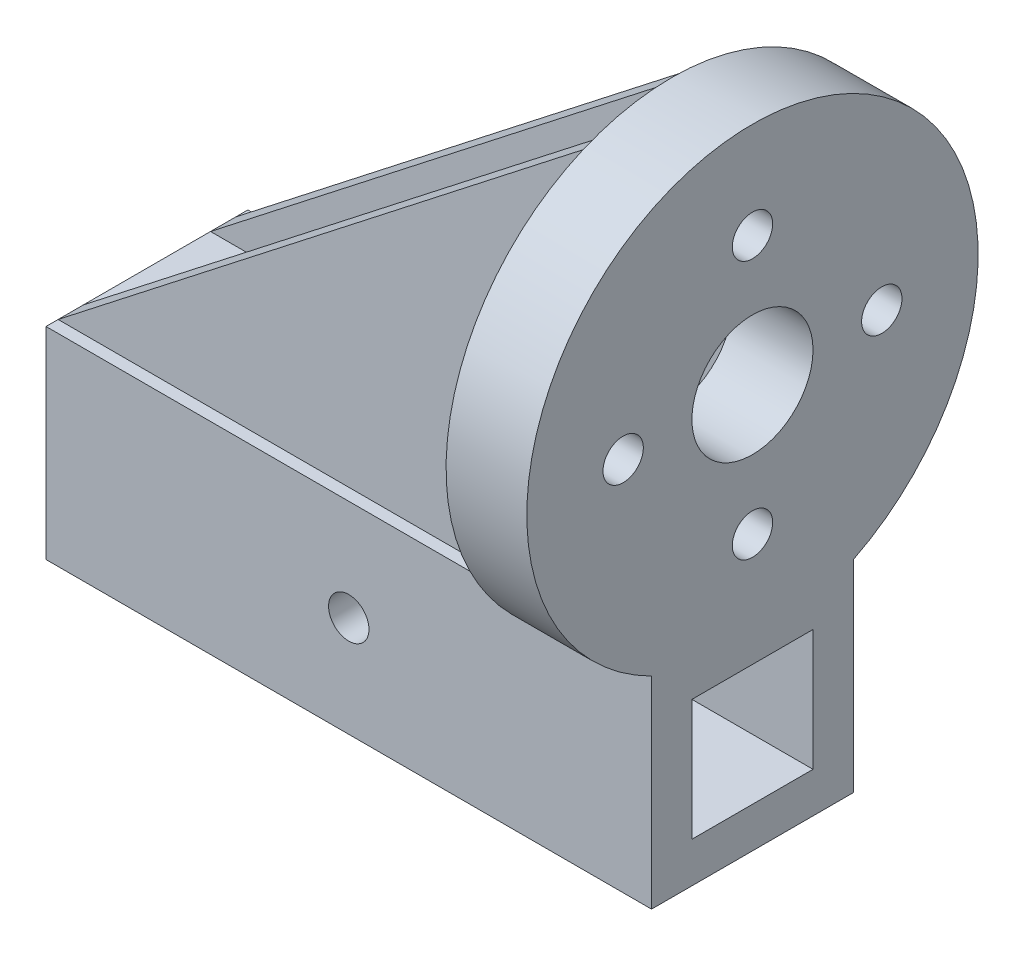
SolidWorks part; units mm, degrees
ref_plane "Front Plane" through (0, 0, 0) normal (0, 0, 1) x (1, 0, 0)
ref_plane "Top Plane" through (0, 0, 0) normal (0, 1, 0) x (1, 0, 0)
ref_plane "Right Plane" through (0, 0, 0) normal (1, 0, 0) x (0, 0, -1)
sketch "Sketch2" plane through (0, 0, 0) normal (0, 1, 0) x (1, 0, 0)
  line L1 (-75, -25) -> (75, -25)
  line L2 (-75, -25) -> (-75, 25)
  line L3 (-75, 25) -> (75, 25)
  line L4 (75, -25) -> (75, 25)
  line L5 (-75, -25) -> (75, 25) construction
  line L6 (-75, 25) -> (75, -25) construction
  point P0 (0, 0)
  dimension "D1" = 50
  dimension "D2" = 150
extrude "Boss-Extrude1" add sketch "Sketch2" along normal blind 50
sketch "Sketch5" plane through (75, 0, 0) normal (1, 0, 0) x (0, 0, -1)
  line L16 (-15, 10) -> (15, 10)
  line L17 (15, 10) -> (15, 40)
  line L18 (15, 40) -> (-15, 40)
  line L19 (-15, 40) -> (-15, 10)
  line L20 (-15, 10) -> (15, 10)
  line L21 (15, 10) -> (15, 40)
  line L22 (15, 40) -> (-15, 40)
  line L23 (-15, 40) -> (-15, 10)
extrude "Cut-Extrude1" cut sketch "Sketch5" against normal through all both and the other way through all
sketch "Sketch7" plane through (75, 0, 0) normal (1, 0, 0) x (0, 0, -1)
  line L0 (0, 100) -> (0, 0) construction
  circle A0 centre (0, 100) radius 55.9017
  circle A1 centre (0, 100) radius 15
  circle A2 centre (0, 132.0304) radius 5
  circle A3 centre (32.0304, 100) radius 5
  circle A4 centre (0, 67.9696) radius 5
  circle A5 centre (-32.0304, 100) radius 5
  point P17 (0, 100)
  dimension "D2" = 30
  dimension "D4" = 10
  dimension "D1" = 100
  dimension "D3" = 4
extrude "Boss-Extrude2" add sketch "Sketch7" against normal blind 20
sketch "Sketch8" plane through (0, 0, -25) normal (0, 0, -1) x (-1, 0, 0)
  line L0 (75, 50) -> (-55, 151.4082)
  line L1 (-55, 151.4082) -> (-55, 50)
  line L2 (-55, 50) -> (75, 50)
  line L3 (-55, 50) -> (-55, 155.9017) construction
  point P6 (-55, 155.9017)
  point P7 (-55, 151.4082)
extrude "Boss-Extrude3" add sketch "Sketch8" against normal blind 6.25 from offset 3 offset against normal yes
sketch "Sketch11" plane through (0, 0, 25) normal (0, 0, 1) x (1, 0, 0)
  circle A0 centre (0, 25) radius 5
  dimension "D1" = 10
extrude "Cut-Extrude2" cut sketch "Sketch11" against normal through all both and the other way through all
ref_plane "Plane1" through (0, 0, 0) normal (0, 0, 1) x (1, 0, 0)
mirror "Mirror1" about plane through (0, 0, 0) normal (0, 0, 1) of "Boss-Extrude3"
equation "\"ss\"= 50"
equation "\"D1@Sketch2\"=\"ss\""
equation "\"rl\"= 150"
equation "\"cr\"= 60"
equation "\"D2@Sketch2\"=\"rl\""
equation "\"D1@Boss-Extrude1\"=\"ss\""
equation "\"o\"= 10"
equation "\"rh\"= 10"
equation "\"D1@Sketch5\"=\"o\""
equation "\"ctb\"= 2 * \"ss\""
equation "\"D1@Sketch7\"=\"ctb\""
equation "\"chc\" = 30"
equation "\"D2@Sketch7\"=\"chc\""
equation "\"D1@Boss-Extrude3\"=\"ss\"/8"
equation "\"D1@Sketch11\"=\"rh\""
equation "\"cha\"= 10"
equation "\"D4@Sketch7\"=\"cha\""
